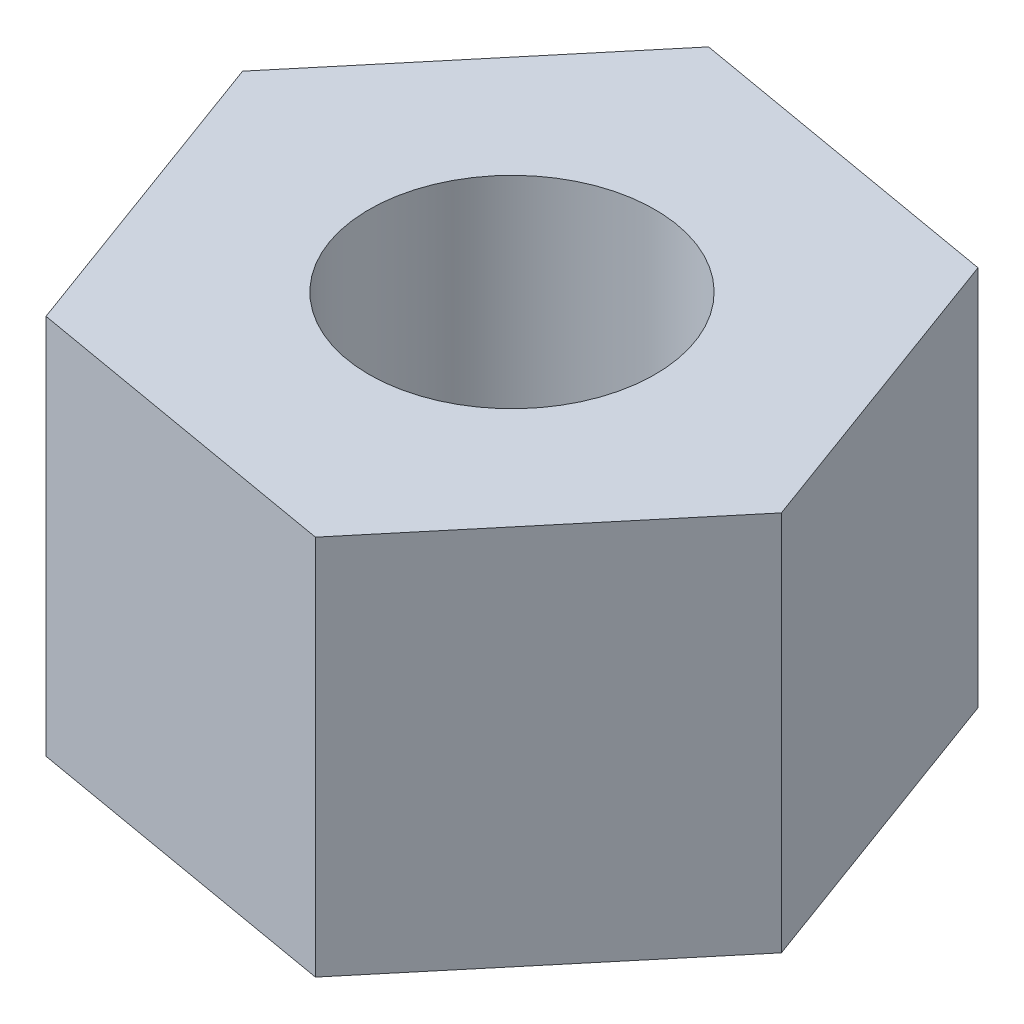
SolidWorks part; units mm, degrees
material "Brass"
ref_plane "Front Plane" through (0, 0, 0) normal (0, 0, 1) x (1, 0, 0)
ref_plane "Top Plane" through (0, 0, 0) normal (0, 1, 0) x (1, 0, 0)
ref_plane "Right Plane" through (0, 0, 0) normal (1, 0, 0) x (0, 0, -1)
sketch "Sketch1" plane through (0, 0, 0) normal (0, 1, 0) x (1, 0, 0)
  line L1 (-0.475, 1.2941) -> (-1.3582, 0.2357)
  line L2 (-1.3582, 0.2357) -> (-0.8832, -1.0584)
  line L3 (-0.8832, -1.0584) -> (0.475, -1.2941)
  line L4 (0.475, -1.2941) -> (1.3582, -0.2357)
  line L5 (1.3582, -0.2357) -> (0.8832, 1.0584)
  line L6 (0.8832, 1.0584) -> (-0.475, 1.2941)
  circle A0 centre (0, 0) radius 1.1938 construction
  dimension "D1" = 2.3876
extrude "Boss-Extrude1" add sketch "Sketch1" along normal blind 1.5875
hole_wizard "#0-80 Tapped Hole1" positions "Sketch2" profile "Sketch3" tap size "#0-80" standard "ANSI Inch" end condition through all
sketch "Sketch2" plane through (0, 1.5875, 0) normal (0, 1, 0) x (1, 0, 0)
  point P0 (0, 0)
sketch "Sketch3" plane through (0, 1.5875, 0) normal (1, 0, 0) x (0, 0, 1)
  line L0 (0, 0) -> (0, 1.5875)
  line L1 (0, 1.5875) -> (0.5956, 1.5875)
  line L2 (0.5956, 1.5875) -> (0.5956, 0)
  line L5 (0.5956, 0) -> (0, 0)
  line L11 (0, -6.35) -> (0, 107.95) construction
  dimension "Thru Tap Drill Dia." = 1.1913
  dimension "Thru Tap Drill Depth" = 1.5875
cosmetic thread "Hole Thread1" parameters "D2"=1.524
